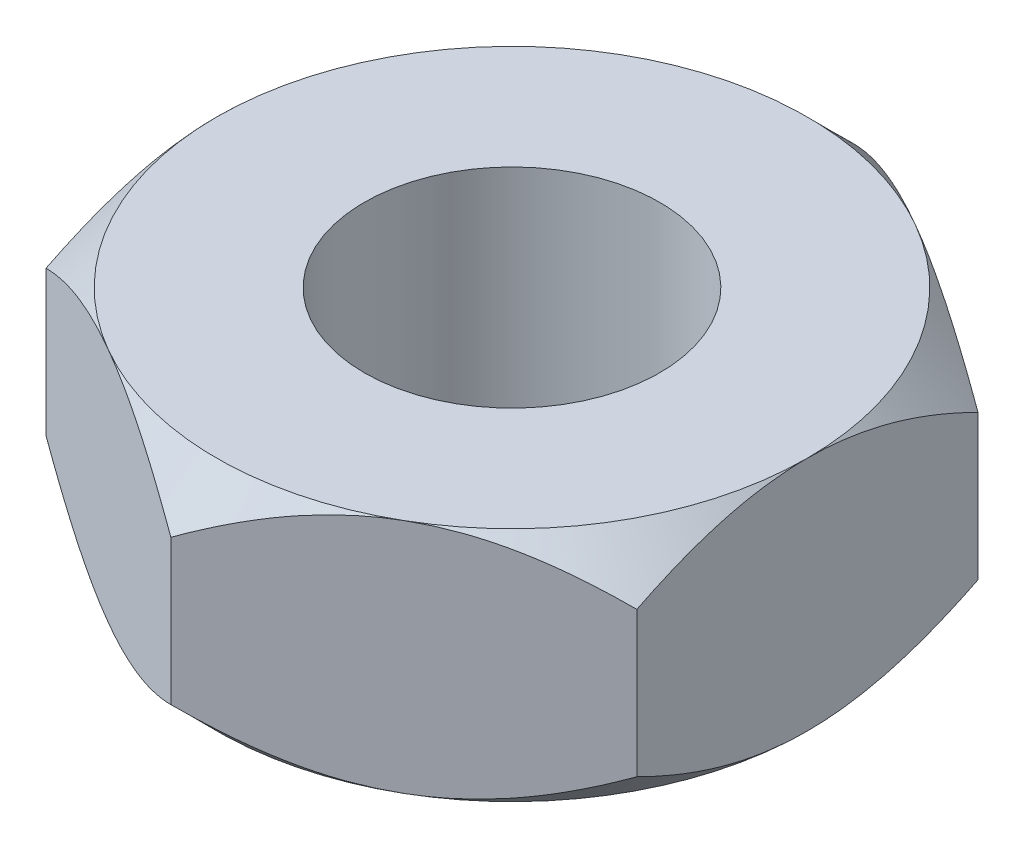
SolidWorks part; units mm, degrees
material "1023 Carbon Steel Sheet (SS)"
ref_plane "Front Plane" through (0, 0, 0) normal (0, 0, 1) x (1, 0, 0)
ref_plane "Top Plane" through (0, 0, 0) normal (0, 1, 0) x (1, 0, 0)
ref_plane "Right Plane" through (0, 0, 0) normal (1, 0, 0) x (0, 0, -1)
sketch "Sketch1" plane through (0, 0, 0) normal (0, 1, 0) x (1, 0, 0)
  line L1 (0, 2.8868) -> (-2.5, 1.4434)
  line L2 (-2.5, 1.4434) -> (-2.5, -1.4434)
  line L3 (-2.5, -1.4434) -> (0, -2.8868)
  line L4 (0, -2.8868) -> (2.5, -1.4434)
  line L5 (2.5, -1.4434) -> (2.5, 1.4434)
  line L6 (2.5, 1.4434) -> (0, 2.8868)
  circle A0 centre (0, 0) radius 2.5 construction
  circle A1 centre (0, 0) radius 1.25
  dimension "D2" = 2.5
  dimension "D1" = 5
extrude "Boss-Extrude1" add sketch "Sketch1" along normal blind 2
sketch "Sketch2" plane through (0, 2, 0) normal (0, 1, 0) x (1, 0, 0)
  circle A0 centre (0, 0) radius 2.5
  dimension "D1" = 5
extrude "Cut-Extrude1" cut sketch "Sketch2" against normal through all draft 45 flip side to cut
sketch "Sketch3" plane through (0, 0, 0) normal (0, -1, 0) x (1, 0, 0)
  circle A0 centre (0, 0) radius 2.5
  dimension "D1" = 5
extrude "Cut-Extrude2" cut sketch "Sketch3" against normal through all draft 45 flip side to cut
